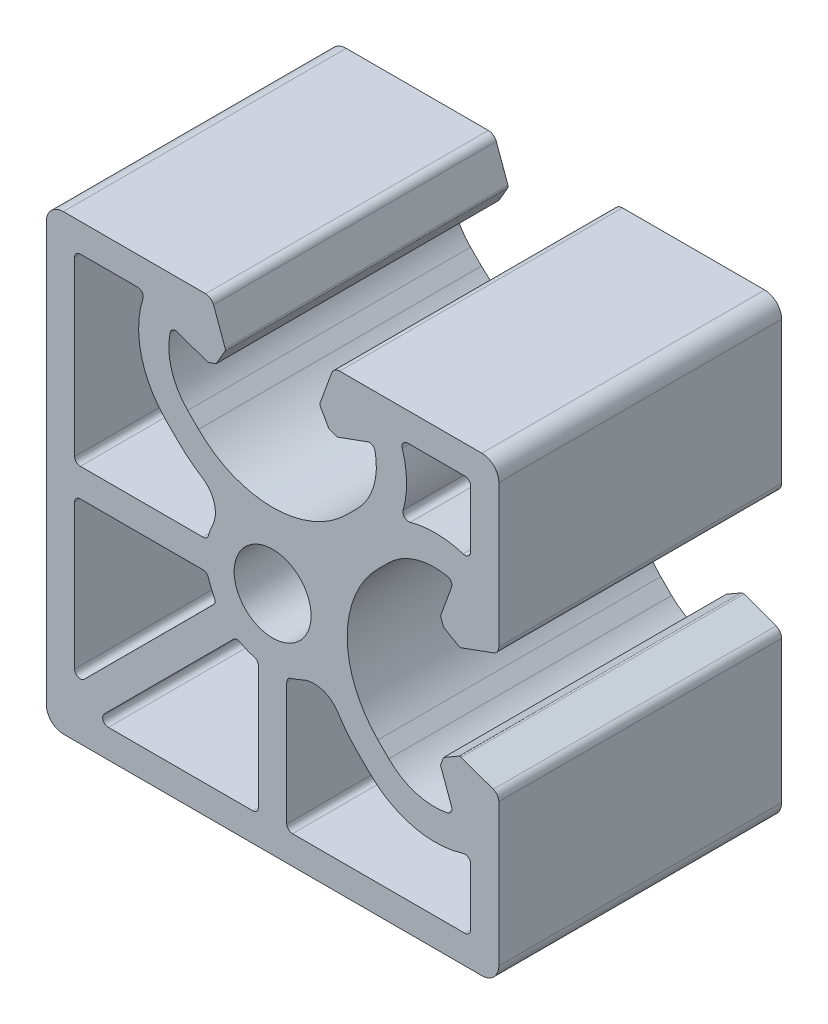
SolidWorks part; units mm, degrees
material "6005-T5"
ref_plane "Front" through (0, 0, 0) normal (0, 0, 1) x (1, 0, 0)
ref_plane "Top" through (0, 0, 0) normal (0, 1, 0) x (1, 0, 0)
ref_plane "Right" through (0, 0, 0) normal (1, 0, 0) x (0, 0, -1)
sketch "Sk Main Extrusion" plane through (0, 0, 0) normal (0, 0, 1) x (1, 0, 0)
  line L0 (-8.3085, 7.4415) -> (-9.4443, 8.5773)
  line L5 (-11.9407, 17.5) -> (-17, 17.5)
  line L6 (-17.5, 17) -> (-17.5, 1.75)
  line L7 (-17, 1.25) -> (-6.1561, 1.25)
  line L8 (17.5, 11.9407) -> (17.5, 17)
  line L9 (17, 17.5) -> (11.9407, 17.5)
  line L10 (-17.5, -1.75) -> (-17.5, -14.5251)
  line L11 (-16.6464, -14.8787) -> (-5.2369, -3.4691)
  line L12 (-6.1561, -1.25) -> (-17, -1.25)
  line L13 (-14.5251, -17.5) -> (-1.75, -17.5)
  line L14 (-1.25, -17) -> (-1.25, -6.1561)
  line L15 (-3.4691, -5.2369) -> (-14.8787, -16.6464)
  line L16 (16.6712, 4.1901) -> (19.5065, 5.2221)
  line L17 (20, 5.9268) -> (20, 18.5)
  line L18 (18.5, 20) -> (5.9268, 20)
  line L19 (5.2221, 19.5065) -> (4.1901, 16.6712)
  line L20 (4.2085, 16.4607) -> (4.9876, 15.1113)
  line L21 (4.9876, 15.1113) -> (5.7185, 14.8453)
  line L22 (5.7185, 14.8453) -> (8.3962, 15.8198)
  line L23 (7.5042, 10.2727) -> (6.5407, 9.3093)
  line L24 (-6.5407, 9.3093) -> (-7.5042, 10.2727)
  line L25 (-8.3962, 15.8198) -> (-5.7185, 14.8453)
  line L26 (-5.7185, 14.8453) -> (-4.9876, 15.1113)
  line L27 (-4.9876, 15.1113) -> (-4.2085, 16.4607)
  line L28 (-4.1901, 16.6712) -> (-5.2221, 19.5065)
  line L29 (-5.9268, 20) -> (-18.5, 20)
  line L30 (-20, 18.5) -> (-20, -18.5)
  line L31 (-18.5, -20) -> (18.5, -20)
  line L32 (20, -18.5) -> (20, -5.9268)
  line L33 (19.5065, -5.2221) -> (16.6712, -4.1901)
  line L34 (16.4607, -4.2085) -> (15.1113, -4.9876)
  line L35 (15.1113, -4.9876) -> (14.8453, -5.7185)
  line L36 (14.8453, -5.7185) -> (15.8198, -8.3962)
  line L37 (10.2727, -7.5042) -> (9.3093, -6.5407)
  line L38 (9.3093, 6.5407) -> (10.2727, 7.5042)
  line L39 (15.8198, 8.3962) -> (14.8453, 5.7185)
  line L40 (14.8453, 5.7185) -> (15.1113, 4.9876)
  line L41 (15.1113, 4.9876) -> (16.4607, 4.2085)
  line L42 (1.75, -17.5) -> (17, -17.5)
  line L43 (17.5, -17) -> (17.5, -11.9407)
  line L44 (8.5773, -9.4443) -> (7.4415, -8.3085)
  line L45 (1.25, -6.1561) -> (1.25, -17)
  arc A0 (-6.1561, 1.25) -> (-5.6751, 1.6133) centre (-6.1561, 1.75) ccw
  arc A1 (-5.3076, 2.5767) -> (-5.6751, 1.6133) centre (0, 0) ccw
  arc A2 (-5.3076, 2.5767) -> (-6.2308, 5.7881) centre (-7.5566, 3.6686) ccw
  arc A3 (-8.3085, 7.4415) -> (-6.2308, 5.7881) centre (0, 15.75) ccw
  arc A4 (-11.464, 16.8492) -> (-9.4443, 8.5773) centre (-3.646, 14.3755) ccw
  arc A5 (-11.464, 16.8492) -> (-11.9407, 17.5) centre (-11.9407, 17) ccw
  arc A6 (-17, 17.5) -> (-17.5, 17) centre (-17, 17) ccw
  arc A7 (-17.5, 1.75) -> (-17, 1.25) centre (-17, 1.75) ccw
  arc A8 (19.5065, 5.2221) -> (20, 5.9268) centre (19.25, 5.9268) ccw
  arc A9 (20, 18.5) -> (18.5, 20) centre (18.5, 18.5) ccw
  arc A10 (5.9268, 20) -> (5.2221, 19.5065) centre (5.9268, 19.25) ccw
  arc A11 (4.1901, 16.6712) -> (4.2085, 16.4607) centre (4.425, 16.5857) ccw
  arc A12 (9.057, 15.4507) -> (8.3962, 15.8198) centre (8.5672, 15.35) ccw
  arc A13 (7.5042, 10.2727) -> (9.057, 15.4507) centre (3.4737, 14.3032) ccw
  arc A14 (-6.5407, 9.3093) -> (6.5407, 9.3093) centre (0, 15.85) ccw
  arc A15 (-9.057, 15.4507) -> (-7.5042, 10.2727) centre (-3.4737, 14.3032) ccw
  arc A16 (-8.3962, 15.8198) -> (-9.057, 15.4507) centre (-8.5672, 15.35) ccw
  arc A17 (-4.2085, 16.4607) -> (-4.1901, 16.6712) centre (-4.425, 16.5857) ccw
  arc A18 (-5.2221, 19.5065) -> (-5.9268, 20) centre (-5.9268, 19.25) ccw
  arc A19 (-18.5, 20) -> (-20, 18.5) centre (-18.5, 18.5) ccw
  arc A20 (-20, -18.5) -> (-18.5, -20) centre (-18.5, -18.5) ccw
  arc A21 (18.5, -20) -> (20, -18.5) centre (18.5, -18.5) ccw
  arc A22 (20, -5.9268) -> (19.5065, -5.2221) centre (19.25, -5.9268) ccw
  arc A23 (16.6712, -4.1901) -> (16.4607, -4.2085) centre (16.5857, -4.425) ccw
  arc A24 (15.4507, -9.057) -> (15.8198, -8.3962) centre (15.35, -8.5672) ccw
  arc A25 (10.2727, -7.5042) -> (15.4507, -9.057) centre (14.3032, -3.4737) ccw
  arc A26 (9.3093, 6.5407) -> (9.3093, -6.5407) centre (15.85, 0) ccw
  arc A27 (15.4507, 9.057) -> (10.2727, 7.5042) centre (14.3032, 3.4737) ccw
  arc A28 (15.8198, 8.3962) -> (15.4507, 9.057) centre (15.35, 8.5672) ccw
  arc A29 (16.4607, 4.2085) -> (16.6712, 4.1901) centre (16.5857, 4.425) ccw
  arc A30 (11.9407, 17.5) -> (11.464, 16.8492) centre (11.9407, 17) ccw
  arc A31 (11.5401, 12.1568) -> (11.464, 16.8492) centre (3.646, 14.3755) ccw
  arc A32 (11.5401, 12.1568) -> (12.1568, 11.5401) centre (12.0215, 12.0215) ccw
  arc A33 (16.8492, 11.464) -> (12.1568, 11.5401) centre (14.3755, 3.646) ccw
  arc A34 (16.8492, 11.464) -> (17.5, 11.9407) centre (17, 11.9407) ccw
  arc A35 (17.5, 17) -> (17, 17.5) centre (17, 17) ccw
  circle A36 centre (0, 0) radius 3.4
  arc A37 (-17, -1.25) -> (-17.5, -1.75) centre (-17, -1.75) ccw
  arc A38 (-17.5, -14.5251) -> (-16.6464, -14.8787) centre (-17, -14.5251) ccw
  arc A39 (-5.2369, -3.4691) -> (-5.1537, -2.8722) centre (-5.5905, -3.1156) ccw
  arc A40 (-5.6751, -1.6133) -> (-5.1537, -2.8722) centre (0, 0) ccw
  arc A41 (-5.6751, -1.6133) -> (-6.1561, -1.25) centre (-6.1561, -1.75) ccw
  arc A42 (-14.8787, -16.6464) -> (-14.5251, -17.5) centre (-14.5251, -17) ccw
  arc A43 (-1.75, -17.5) -> (-1.25, -17) centre (-1.75, -17) ccw
  arc A44 (-1.25, -6.1561) -> (-1.6133, -5.6751) centre (-1.75, -6.1561) ccw
  arc A45 (-2.8722, -5.1537) -> (-1.6133, -5.6751) centre (0, 0) ccw
  arc A46 (-2.8722, -5.1537) -> (-3.4691, -5.2369) centre (-3.1156, -5.5905) ccw
  arc A47 (1.25, -17) -> (1.75, -17.5) centre (1.75, -17) ccw
  arc A48 (17, -17.5) -> (17.5, -17) centre (17, -17) ccw
  arc A49 (17.5, -11.9407) -> (16.8492, -11.464) centre (17, -11.9407) ccw
  arc A50 (8.5773, -9.4443) -> (16.8492, -11.464) centre (14.3755, -3.646) ccw
  arc A51 (5.7881, -6.2308) -> (7.4415, -8.3085) centre (15.75, 0) ccw
  arc A52 (5.7881, -6.2308) -> (2.5767, -5.3076) centre (3.6686, -7.5566) ccw
  arc A53 (1.6133, -5.6751) -> (2.5767, -5.3076) centre (0, 0) ccw
  arc A54 (1.6133, -5.6751) -> (1.25, -6.1561) centre (1.75, -6.1561) ccw
extrude "Main Extrusion" add sketch "Sk Main Extrusion" against normal blind 25
sketch "Threaded Insert Mate Sketch" plane through (0, 0, 0) normal (0, 0, 1) x (1, 0, 0)
  circle A0 centre (0, 12.7) radius 5.6515
  circle A1 centre (12.7, 0) radius 5.6515
  circle A2 centre (0, -12.7) radius 5.6515
  circle A3 centre (-12.7, 0) radius 5.6515
  circle A4 centre (0, 0) radius 3.4 construction
  point P2 (0, 0)
  point P12 (0, 0)
  dimension "D2" = 11.303
  dimension "D1" = 12.7
  dimension "D3" = 4
equation "\"Weight kg\"= round ( \"SW-Mass\" , 2 )"
equation "\"Weight lbs\"= round ( \"SW-Mass\" * 2.2046 , 2 )"
equation "\"Length mm\"= round ( \"Length@Main Extrusion\" , 2 )"
equation "\"Length in\"= round ( \"Length@Main Extrusion\" / 25.4 , 3 )"
